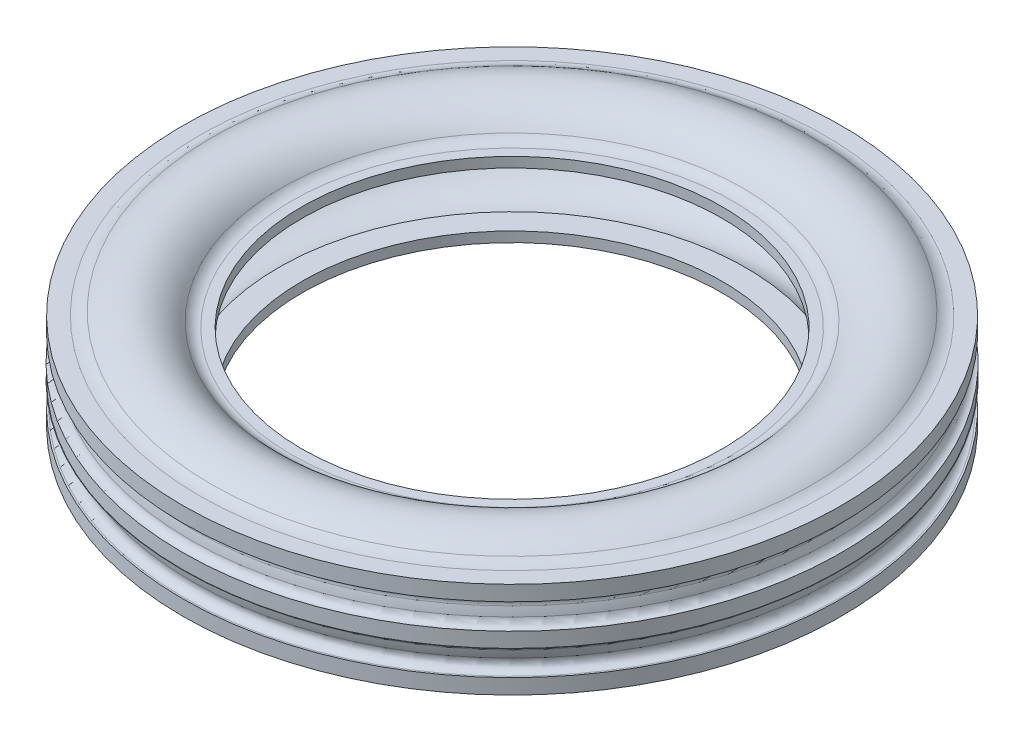
SolidWorks part; units mm, degrees
ref_plane "Front Plane" through (0, 0, 0) normal (0, 0, 1) x (1, 0, 0)
ref_plane "Top Plane" through (0, 0, 0) normal (0, 1, 0) x (1, 0, 0)
ref_plane "Right Plane" through (0, 0, 0) normal (1, 0, 0) x (0, 0, -1)
sketch "Sketch5" plane through (0, 433528.713, 0) normal (0, 0, -1) x (-1, 0, 0)
  line L0 (-231.3394, -433501.713) -> (-208, -433501.713)
  line L1 (-208, -433501.713) -> (-208, -433491.713)
  line L2 (-208, -433491.713) -> (-218.04, -433491.713)
  line L3 (-309.3249, -433481.213) -> (-326, -433481.213)
  line L4 (-326, -433481.213) -> (-326, -433496.213)
  line L5 (-326, -433496.213) -> (-324.3956, -433496.213)
  line L6 (-326.38, -433521.213) -> (-326, -433521.213)
  line L7 (-326, -433521.213) -> (-326, -433536.213)
  line L8 (-326, -433536.213) -> (-326.38, -433536.213)
  line L9 (-324.3956, -433561.213) -> (-326, -433561.213)
  line L10 (-326, -433561.213) -> (-326, -433576.213)
  line L11 (-326, -433576.213) -> (-309.3249, -433576.213)
  line L12 (-218.04, -433565.713) -> (-208, -433565.713)
  line L13 (-208, -433565.713) -> (-208, -433555.713)
  line L14 (-208, -433555.713) -> (-231.3394, -433555.713)
  line L15 (0, -433559.713) -> (0, -433528.713) construction
  line L16 (-234.6808, -433528.713) -> (0, -433528.713) construction
  arc A0 (-228.9688, -433486.463) -> (-297.5178, -433477.3558) centre (-268, -433517.713) ccw
  arc A1 (-297.5178, -433477.3558) -> (-309.3249, -433481.213) centre (-309.3249, -433461.213) cw
  arc A2 (-324.3956, -433496.213) -> (-316.6782, -433506.3205) centre (-324.3956, -433504.213) cw
  arc A4 (-316.6782, -433506.3205) -> (-318.4919, -433514.5463) centre (-234.6808, -433528.713) ccw
  arc A5 (-318.4919, -433514.5463) -> (-326.38, -433521.213) centre (-326.38, -433513.213) cw
  arc A6 (-326.38, -433536.213) -> (-318.4919, -433542.8796) centre (-326.38, -433544.213) cw
  arc A7 (-318.4919, -433542.8796) -> (-316.6782, -433551.1054) centre (-234.6808, -433528.713) ccw
  arc A8 (-228.9688, -433570.963) -> (-218.04, -433565.713) centre (-218.04, -433579.713) cw
  arc A9 (-316.6782, -433551.1054) -> (-324.3956, -433561.213) centre (-324.3956, -433553.213) cw
  arc A10 (-309.3249, -433576.213) -> (-297.5178, -433580.0701) centre (-309.3249, -433596.213) cw
  arc A11 (-297.5178, -433580.0701) -> (-228.9688, -433570.963) centre (-268, -433539.713) ccw
  arc A12 (-231.3394, -433555.713) -> (-307.02, -433548.513) centre (-268, -433539.713) cw
  arc A13 (-307.02, -433548.513) -> (-307.02, -433508.913) centre (-234.6808, -433528.713) cw
  arc A14 (-307.02, -433508.913) -> (-231.3394, -433501.713) centre (-268, -433517.713) cw
  arc A15 (-228.9688, -433486.463) -> (-218.04, -433491.713) centre (-218.04, -433477.713) ccw
  point P18 (-225.2917, -433565.713)
  point P41 (-326, -433528.713)
  point P46 (-225.2917, -433491.713)
  dimension "D7" = 75
  dimension "D8" = 50
  dimension "D9" = 40
  dimension "D10" = 8
  dimension "D11" = 14
  dimension "D15" = 10
  dimension "D1" = 208
  dimension "D2" = 27
  dimension "D3" = 11
  dimension "D4" = 60
  dimension "D5" = 10
  dimension "D6" = 19.8
  dimension "D12" = 47.5
  dimension "D13" = 15
  dimension "D14" = 32.5
  dimension "D16" = 118
  dimension "D17" = 67.5
  dimension "D18" = 15.5
  dimension "D19" = 24.5
revolve "Revolve2" add sketch "Sketch5" angle 360 about L15
